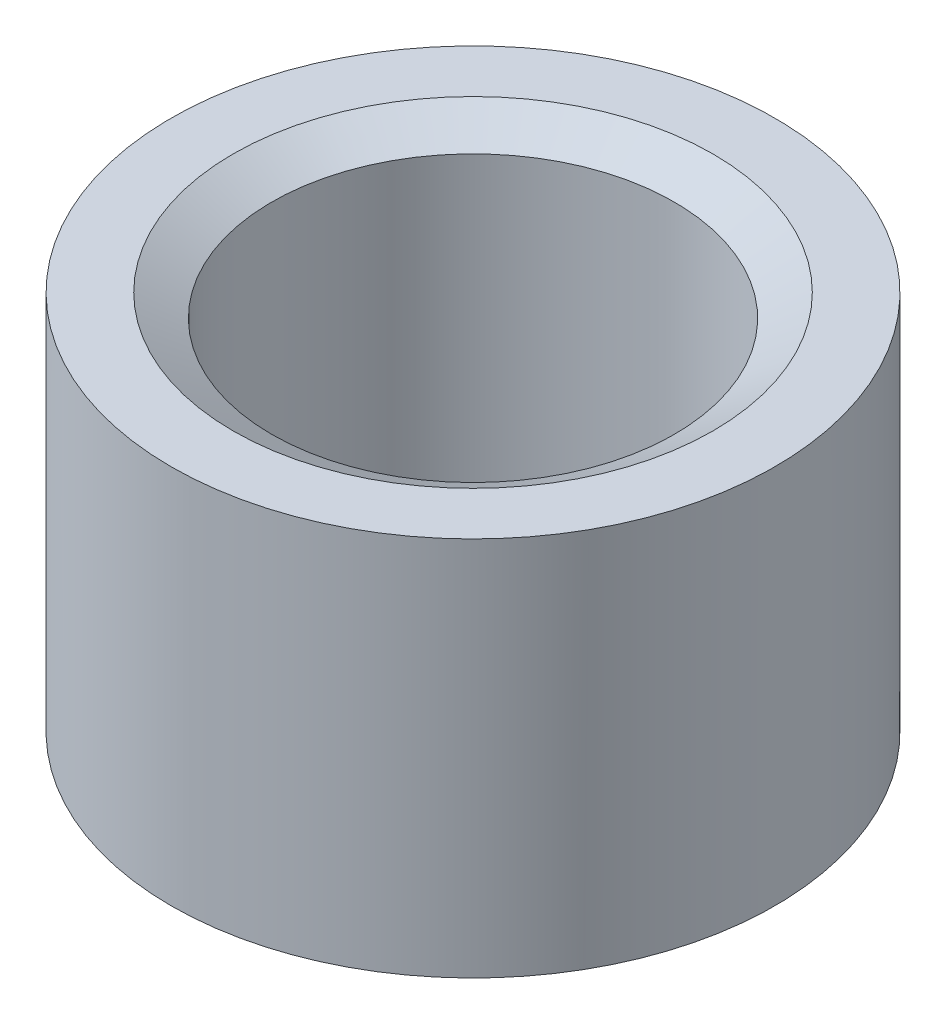
SolidWorks part; units mm, degrees
ref_plane "Front Plane" through (0, 0, 0) normal (0, 0, 1) x (1, 0, 0)
ref_plane "Top Plane" through (0, 0, 0) normal (0, 1, 0) x (1, 0, 0)
ref_plane "Right Plane" through (0, 0, 0) normal (1, 0, 0) x (0, 0, -1)
sketch "Sketch1" plane through (0, 0, 0) normal (0, 0, -1) x (1, 0, 0)
  line L0 (0, 0) -> (0, 3.175) construction
  line L2 (2.3813, 0) -> (1.5875, 0)
  line L3 (2.3813, 0) -> (2.3813, 3.175)
  line L4 (2.3813, 3.175) -> (1.5875, 3.175)
  line L5 (1.5875, 0) -> (1.5875, 3.175)
  dimension "D1" = 3.175
  dimension "D2" = 4.7625
  dimension "D3" = 3.175
revolve "Revolve1" add sketch "Sketch1" angle 360 about L0
chamfer "Chamfer1" distance 0.3048 angle 30 2 edges at (0, 0, 1.5875) (0, -3.175, 2.3813)
